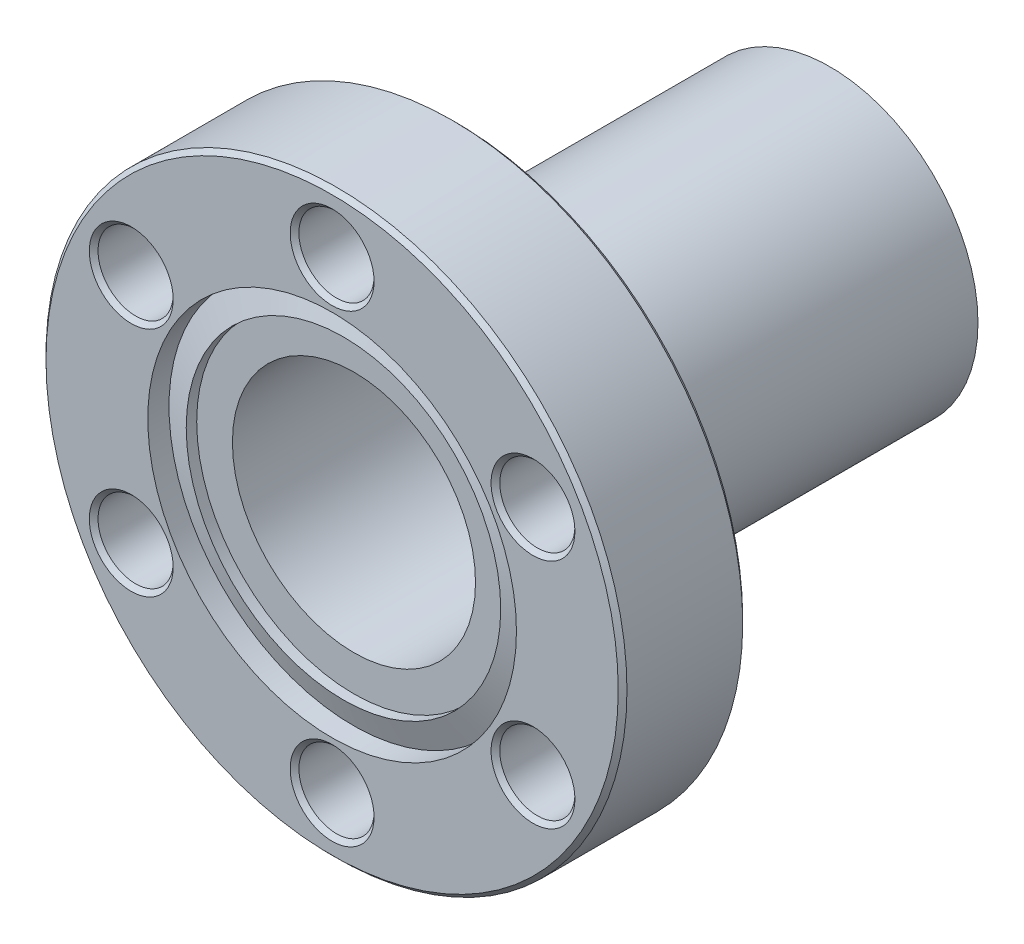
SolidWorks part; units mm, degrees
ref_plane "Front Plane" through (0, 0, 0) normal (0, 0, 1) x (1, 0, 0)
ref_plane "Top Plane" through (0, 0, 0) normal (0, 1, 0) x (1, 0, 0)
ref_plane "Right Plane" through (0, 0, 0) normal (1, 0, 0) x (0, 0, -1)
sketch "Sketch1" plane through (0, 0, 0) normal (0, 1, 0) x (1, 0, 0)
  line L0 (16.891, 7.239) -> (0, 7.239)
  line L1 (0, 7.239) -> (0, 1.27)
  line L2 (0, 1.27) -> (5.3211, 1.27)
  line L3 (6.7947, 1.27) -> (9.144, 1.27)
  line L4 (9.144, 1.27) -> (9.144, 0.6604)
  line L5 (9.144, 0.6604) -> (10.7188, 1.2336)
  line L6 (10.7188, 1.2336) -> (10.7188, 0)
  line L7 (10.7188, 0) -> (16.891, 0)
  line L8 (16.891, 0) -> (16.891, 7.239)
  line L9 (0, 7.239) -> (0, 0) construction
  arc A0 (5.3211, 1.27) -> (6.7947, 1.27) centre (6.0579, 1.0757) cw
revolve "Revolve1" add sketch "Sketch1" angle 360 about L9
hole_wizard "M8 Clearance Hole1" positions "Sketch3" profile "Sketch2" hole size "M8" standard "ANSI Metric"
sketch "Sketch3" plane through (0, 0, -7.239) normal (0, 0, -1) x (-1, 0, 0)
  point P0 (0, 0)
sketch "Sketch2" plane through (0, 0, -7.239) normal (1, 0, 0) x (0, 1, 0)
  line L0 (0, 0) -> (0, 7.239)
  line L1 (0, 7.239) -> (4.7879, 7.239)
  line L2 (4.7879, 7.239) -> (4.7879, 0)
  line L5 (4.7879, 0) -> (0, 0)
  line L11 (0, -6.35) -> (0, 107.95) construction
  dimension "Thru Hole Dia." = 9.5758
  dimension "Thru Hole Depth" = 7.239
hole_wizard "M4 Clearance Hole1" positions "Sketch5" profile "Sketch4" hole size "M4" standard "ANSI Metric"
sketch "Sketch5" plane through (0, 0, 0) normal (0, 0, 1) x (1, 0, 0)
  point P0 (11.6804, 6.7437)
  point P1 (0, -13.4874)
  point P2 (-11.6804, -6.7437)
  point P3 (-11.6804, 6.7437)
sketch "Sketch4" plane through (11.6804, 6.7437, 0) normal (1, 0, 0) x (0, -1, 0)
  line L0 (0, 0) -> (0, 7.239)
  line L1 (0, 7.239) -> (2.1844, 7.239)
  line L2 (2.1844, 7.239) -> (2.1844, 0)
  line L5 (2.1844, 0) -> (0, 0)
  line L11 (0, -6.35) -> (0, 107.95) construction
  dimension "Thru Hole Dia." = 4.3688
  dimension "Thru Hole Depth" = 7.239
hole_wizard "M4 Clearance Hole2" positions "Sketch7" profile "Sketch6" hole size "M4" standard "ANSI Metric"
sketch "Sketch7" plane through (0, 0, -7.239) normal (0, 0, -1) x (-1, 0, 0)
  point P0 (0, 13.4874)
  point P1 (-11.6804, -6.7437)
sketch "Sketch6" plane through (0, 13.4874, -7.239) normal (1, 0, 0) x (0, 1, 0)
  line L0 (0, 0) -> (0, 7.239)
  line L1 (0, 7.239) -> (2.1844, 7.239)
  line L2 (2.1844, 7.239) -> (2.1844, 0)
  line L5 (2.1844, 0) -> (0, 0)
  line L11 (0, -6.35) -> (0, 107.95) construction
  dimension "Thru Hole Dia." = 4.3688
  dimension "Thru Hole Depth" = 7.239
chamfer "Chamfer1" distance 0.254 angle 45 14 edges at (16.891, 0, -7.239) (2.1844, -13.4874, -7.239) (13.8648, 6.7437, -7.239) (-2.1844, 13.4874, 0) (-9.496, 6.7437, -7.239) (13.8648, 6.7437, 0) (-2.1844, 13.4874, -7.239) (9.496, -6.7437, 0) (9.496, -6.7437, -7.239) (2.1844, -13.4874, 0) (-9.496, -6.7437, -7.239) (-9.496, -6.7437, 0) (16.891, 0, 0) (-9.496, 6.7437, 0)
sketch "Sketch8" plane through (0, 0, -7.239) normal (0, 0, -1) x (-1, 0, 0)
  circle A0 centre (0, 0) radius 8.6006
extrude "Boss-Extrude1" add sketch "Sketch8" along normal blind 21.717
sketch "Sketch9" plane through (0, 0, -28.956) normal (0, 0, -1) x (-1, 0, 0)
  circle A0 centre (0, 0) radius 7.0681
extrude "Cut-Extrude1" cut sketch "Sketch9" against normal through all
